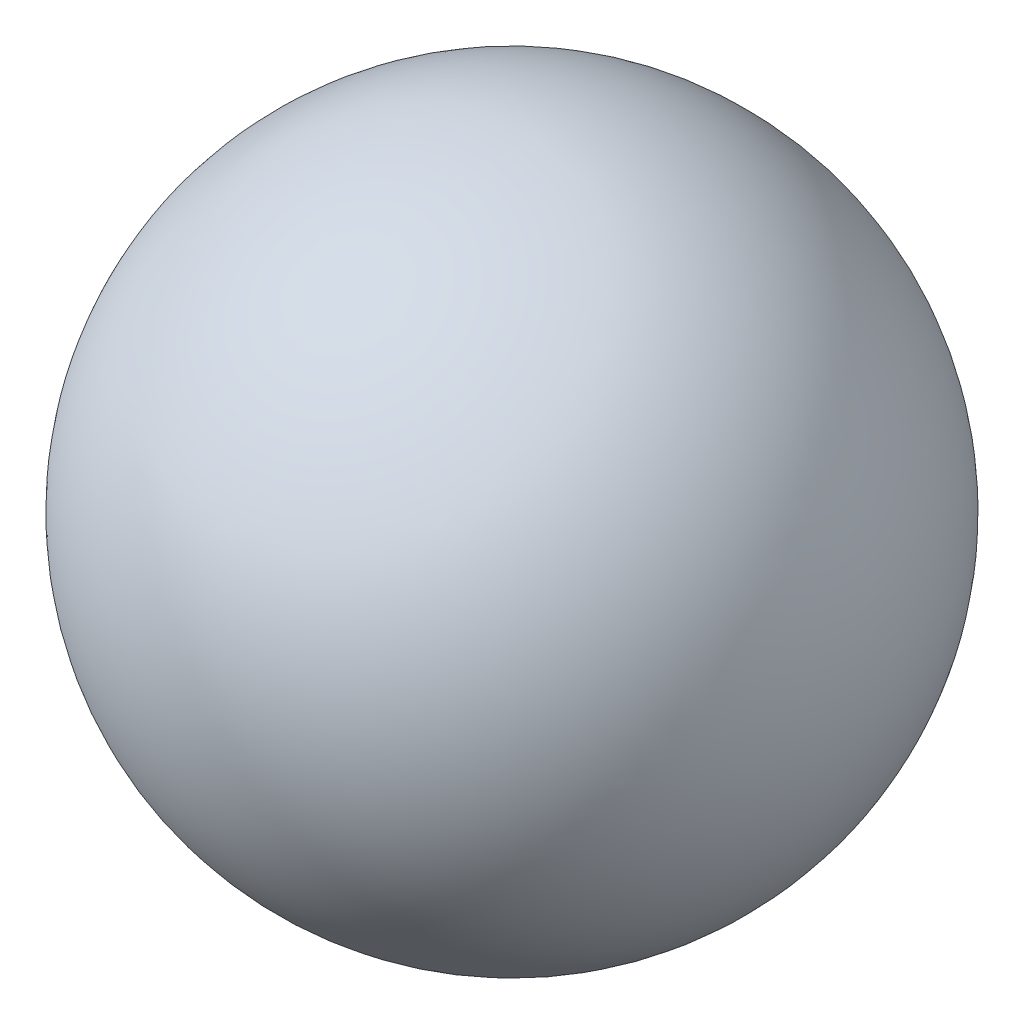
SolidWorks part; units mm, degrees
ref_plane "Front Plane" through (0, 0, 0) normal (0, 0, 1) x (1, 0, 0)
ref_plane "Top Plane" through (0, 0, 0) normal (0, 1, 0) x (1, 0, 0)
ref_plane "Right Plane" through (0, 0, 0) normal (1, 0, 0) x (0, 0, -1)
ref_plane "Plane1" through (0, 0, 0) normal (0, 0, 1) x (1, 0, 0)
sketch "Sketch1" plane through (0, 0, 0) normal (0, 0, 1) x (1, 0, 0)
  line L0 (1.05, 0) -> (-1.05, 0)
  line L1 (1.05, 0) -> (-1.05, 0) construction
  arc A0 (-1.05, 0) -> (1.05, 0) centre (0, 0) cw
revolve "Revolve1" add sketch "Sketch1" angle 360 about L1
